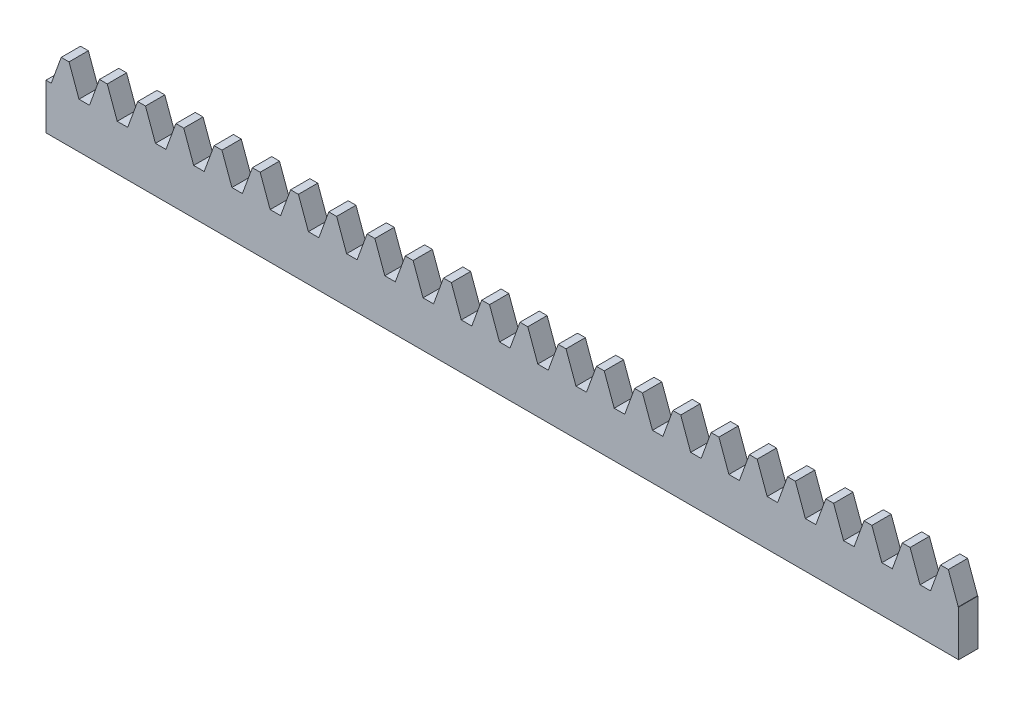
SolidWorks part; units mm, degrees
extrude "Blank" add sketch "BlankSke" against normal blind 10
sketch "BlankSke" plane through (0, 0, 0) normal (0, 0, 1) x (1, 0, 0)
  line L1 (0, 0) -> (150, 0)
  line L2 (0, 0) -> (0, 12)
  line L3 (0, 12) -> (150, 12)
  line L4 (150, 0) -> (150, 12)
  dimension "Length" = 150
  dimension "Blank_height" = 12
ref_plane "Plane1" through (0, 0, 0) normal (0, 0, 1) x (1, 0, 0)
ref_plane "Plane2" through (0, 0, 0) normal (0, 1, 0) x (1, 0, 0)
ref_plane "Plane3" through (0, 0, 0) normal (1, 0, 0) x (0, 0, -1)
sketch "HoldingSke" plane through (0, 0, 0) normal (0, 1, 0) x (1, 0, 0)
  line L0 (0, 0) -> (0.0696, 0.4951)
  line L1 (-15, 0) -> (100, 0) construction
  line L2 (0, 0) -> (-2.1039, 2.3779)
  line L3 (0, 0) -> (-11.863, 4.5341)
  line L4 (0, 0) -> (7.8269, 3.6497)
  line L5 (0, 0) -> (-23.7986, -8.8762)
  line L6 (0, 0) -> (-10.5278, -7.1032)
  line L9 (-71.009, 38.7566) -> (69.9449, 90.0596)
  line L10 (-76.2, 4.3779) -> (-66.2, 4.3779)
  line L11 (0, 0) -> (-10, 0)
  line L12 (-76.2, 101.6) -> (-76.133, 101.6)
  line L13 (24.9733, 27.94) -> (52.9518, 28.4284)
  line L14 (24.9733, 27.94) -> (24.9743, 27.94)
  line L15 (24.9733, 27.94) -> (100.4006, 29.5858)
  circle A0 centre (0, 0) radius 19.05
  circle A1 centre (0, 0) radius 5
  circle A2 centre (0, 0) radius 12.7
  dimension "MPH" = 10
  dimension "Diameter" = 38.1
  dimension "Num_teeth" = 25
  dimension "Pitch" = 0.5
  dimension "Show_teeth" = 998
  dimension "Thickness" = 12.7
  dimension "Ap" = 20
  dimension "Pitch_height" = 10
  dimension "Width" = 10
  dimension "Backlash" = 0.067
  dimension "Addendum_fac" = 1
  dimension "Dedendum_fac" = 1.25
  dimension "Clearance_fac" = 0.25
  dimension "Dedendum_add" = 0.001
  dimension "Length" = 150
  dimension "Module" = 2
sketch "TooCutSkeIll" plane through (0, 0, 0) normal (0, 0, 1) x (1, 0, 0)
  line L0 (-2.4806, 11.9474) -> (-0.9819, 7.8296)
  line L1 (-0.5111, 7.5) -> (0.5111, 7.5)
  line L2 (0.9819, 7.8296) -> (2.4806, 11.9474)
  line L3 (150, 12) -> (0, 12) construction
  line L4 (0, 0) -> (0, 64.897) construction
  line L5 (-13.208, 10) -> (12.954, 10) construction
  line L6 (0, 0) -> (150, 0) construction
  line L7 (1.7718, 10) -> (1.7718, 48.7463) construction
  line L8 (-1.7718, 10) -> (-1.7718, 48.7463) construction
  line L9 (2.5558, 12) -> (2.5558, 12.0254)
  line L10 (-2.5558, 12) -> (-2.5558, 12.0254)
  line L11 (-2.5558, 12.0254) -> (2.5558, 12.0254)
  arc A0 (0.5111, 7.5) -> (0.9819, 7.8296) centre (0.5111, 8.001) ccw
  arc A1 (-0.9819, 7.8296) -> (-0.5111, 7.5) centre (-0.5111, 8.001) ccw
  arc A2 (2.5558, 12) -> (2.4806, 11.9474) centre (2.5558, 11.92) ccw
  arc A3 (-2.4806, 11.9474) -> (-2.5558, 12) centre (-2.5558, 11.92) ccw
  dimension "Pitch_height" = 10
  dimension "Addendum_plus" = 2.0254
  dimension "Pressure_angle" = 20
  dimension "Gap_width" = 3.5436
  dimension "Dedendum" = 2.5
extrude "ToothCutIll" [suppressed] cut sketch "TooCutSkeIll" against normal through all
sketch "TooCutSkeSim" plane through (0, 0, 0) normal (0, 0, 1) x (1, 0, 0)
  line L0 (0.8619, 7.5) -> (-0.8619, 7.5)
  line L1 (2.509, 12.0254) -> (0.8619, 7.5)
  line L2 (0, 17.4625) -> (0, 53.467) construction
  line L3 (2.509, 12.0254) -> (-2.509, 12.0254)
  line L6 (-2.509, 12.0254) -> (-0.8619, 7.5)
  line L9 (-1.7718, 10) -> (1.7718, 10) construction
  line L10 (0, 0) -> (150, 0) construction
  line L11 (1.7718, 10) -> (1.7718, 53.467) construction
  line L12 (-1.7718, 10) -> (-1.7718, 53.467) construction
  dimension "Pitch_height" = 10
  dimension "Addendum_plus" = 2.0254
  dimension "Pressure_angle" = 20
  dimension "Gap_width" = 3.5436
  dimension "Dedendum" = 2.5
extrude "ToothCutSim" cut sketch "TooCutSkeSim" against normal through all
pattern_linear "TeethCuts" count 25 spacing 6.2832 along (1, 0, 0) of "ToothCutIll", "ToothCutSim"
sketch "Sketch1" plane through (0, 0, 0) normal (0, 0, 1) x (1, 0, 0)
  line L100 (150, 7.5) -> (149.9346, 7.5)
  line L101 (149.9346, 7.5) -> (148.2967, 12)
  line L102 (148.2967, 12) -> (147.013, 12)
  line L103 (147.013, 12) -> (145.3751, 7.5)
  line L104 (145.3751, 7.5) -> (143.6514, 7.5)
  line L105 (143.6514, 7.5) -> (142.0135, 12)
  line L106 (142.0135, 12) -> (140.7298, 12)
  line L107 (140.7298, 12) -> (139.0919, 7.5)
  line L108 (139.0919, 7.5) -> (137.3682, 7.5)
  line L109 (137.3682, 7.5) -> (135.7303, 12)
  line L110 (135.7303, 12) -> (134.4466, 12)
  line L111 (134.4466, 12) -> (132.8088, 7.5)
  line L112 (132.8088, 7.5) -> (131.085, 7.5)
  line L113 (131.085, 7.5) -> (129.4472, 12)
  line L114 (129.4472, 12) -> (128.1634, 12)
  line L115 (128.1634, 12) -> (126.5256, 7.5)
  line L116 (126.5256, 7.5) -> (124.8018, 7.5)
  line L117 (124.8018, 7.5) -> (123.164, 12)
  line L118 (123.164, 12) -> (121.8803, 12)
  line L119 (121.8803, 12) -> (120.2424, 7.5)
  line L120 (120.2424, 7.5) -> (118.5186, 7.5)
  line L121 (118.5186, 7.5) -> (116.8808, 12)
  line L122 (116.8808, 12) -> (115.5971, 12)
  line L123 (115.5971, 12) -> (113.9592, 7.5)
  line L124 (113.9592, 7.5) -> (112.2355, 7.5)
  line L125 (112.2355, 7.5) -> (110.5976, 12)
  line L126 (110.5976, 12) -> (109.3139, 12)
  line L127 (109.3139, 12) -> (107.676, 7.5)
  line L128 (107.676, 7.5) -> (105.9523, 7.5)
  line L129 (105.9523, 7.5) -> (104.3144, 12)
  line L130 (104.3144, 12) -> (103.0307, 12)
  line L131 (103.0307, 12) -> (101.3928, 7.5)
  line L132 (101.3928, 7.5) -> (99.6691, 7.5)
  line L133 (99.6691, 7.5) -> (98.0312, 12)
  line L134 (98.0312, 12) -> (96.7475, 12)
  line L135 (96.7475, 12) -> (95.1097, 7.5)
  line L136 (95.1097, 7.5) -> (93.3859, 7.5)
  line L137 (93.3859, 7.5) -> (91.748, 12)
  line L138 (91.748, 12) -> (90.4643, 12)
  line L139 (90.4643, 12) -> (88.8265, 7.5)
  line L140 (88.8265, 7.5) -> (87.1027, 7.5)
  line L141 (87.1027, 7.5) -> (85.4649, 12)
  line L142 (85.4649, 12) -> (84.1811, 12)
  line L143 (84.1811, 12) -> (82.5433, 7.5)
  line L144 (82.5433, 7.5) -> (80.8195, 7.5)
  line L145 (80.8195, 7.5) -> (79.1817, 12)
  line L146 (79.1817, 12) -> (77.898, 12)
  line L147 (77.898, 12) -> (76.2601, 7.5)
  line L148 (76.2601, 7.5) -> (74.5364, 7.5)
  line L149 (74.5364, 7.5) -> (72.8985, 12)
  line L150 (72.8985, 12) -> (71.6148, 12)
  line L151 (71.6148, 12) -> (69.9769, 7.5)
  line L152 (69.9769, 7.5) -> (68.2532, 7.5)
  line L153 (68.2532, 7.5) -> (66.6153, 12)
  line L154 (66.6153, 12) -> (65.3316, 12)
  line L155 (65.3316, 12) -> (63.6937, 7.5)
  line L156 (63.6937, 7.5) -> (61.97, 7.5)
  line L157 (61.97, 7.5) -> (60.3321, 12)
  line L158 (60.3321, 12) -> (59.0484, 12)
  line L159 (59.0484, 12) -> (57.4105, 7.5)
  line L160 (57.4105, 7.5) -> (55.6868, 7.5)
  line L161 (55.6868, 7.5) -> (54.0489, 12)
  line L162 (54.0489, 12) -> (52.7652, 12)
  line L163 (52.7652, 12) -> (51.1274, 7.5)
  line L164 (51.1274, 7.5) -> (49.4036, 7.5)
  line L165 (49.4036, 7.5) -> (47.7657, 12)
  line L166 (47.7657, 12) -> (46.482, 12)
  line L167 (46.482, 12) -> (44.8442, 7.5)
  line L168 (44.8442, 7.5) -> (43.1204, 7.5)
  line L169 (43.1204, 7.5) -> (41.4826, 12)
  line L170 (41.4826, 12) -> (40.1988, 12)
  line L171 (40.1988, 12) -> (38.561, 7.5)
  line L172 (38.561, 7.5) -> (36.8372, 7.5)
  line L173 (36.8372, 7.5) -> (35.1994, 12)
  line L174 (35.1994, 12) -> (33.9157, 12)
  line L175 (33.9157, 12) -> (32.2778, 7.5)
  line L176 (32.2778, 7.5) -> (30.5541, 7.5)
  line L177 (30.5541, 7.5) -> (28.9162, 12)
  line L178 (28.9162, 12) -> (27.6325, 12)
  line L179 (27.6325, 12) -> (25.9946, 7.5)
  line L180 (25.9946, 7.5) -> (24.2709, 7.5)
  line L181 (24.2709, 7.5) -> (22.633, 12)
  line L182 (22.633, 12) -> (21.3493, 12)
  line L183 (21.3493, 12) -> (19.7114, 7.5)
  line L184 (19.7114, 7.5) -> (17.9877, 7.5)
  line L185 (17.9877, 7.5) -> (16.3498, 12)
  line L186 (16.3498, 12) -> (15.0661, 12)
  line L187 (15.0661, 12) -> (13.4282, 7.5)
  line L188 (13.4282, 7.5) -> (11.7045, 7.5)
  line L189 (11.7045, 7.5) -> (10.0666, 12)
  line L190 (10.0666, 12) -> (8.7829, 12)
  line L191 (8.7829, 12) -> (7.1451, 7.5)
  line L192 (7.1451, 7.5) -> (5.4213, 7.5)
  line L193 (5.4213, 7.5) -> (3.7834, 12)
  line L194 (3.7834, 12) -> (2.4997, 12)
  line L195 (2.4997, 12) -> (0.8619, 7.5)
  line L196 (0.8619, 7.5) -> (0, 7.5)
  line L197 (0, 7.5) -> (0, 0)
  line L198 (0, 0) -> (150, 0)
  line L199 (150, 0) -> (150, 7.5)
  line L200 (150, 7.5) -> (149.9346, 7.5)
  line L201 (149.9346, 7.5) -> (148.2967, 12)
  line L202 (148.2967, 12) -> (147.013, 12)
  line L203 (147.013, 12) -> (145.3751, 7.5)
  line L204 (145.3751, 7.5) -> (143.6514, 7.5)
  line L205 (143.6514, 7.5) -> (142.0135, 12)
  line L206 (142.0135, 12) -> (140.7298, 12)
  line L207 (140.7298, 12) -> (139.0919, 7.5)
  line L208 (139.0919, 7.5) -> (137.3682, 7.5)
  line L209 (137.3682, 7.5) -> (135.7303, 12)
  line L210 (135.7303, 12) -> (134.4466, 12)
  line L211 (134.4466, 12) -> (132.8088, 7.5)
  line L212 (132.8088, 7.5) -> (131.085, 7.5)
  line L213 (131.085, 7.5) -> (129.4472, 12)
  line L214 (129.4472, 12) -> (128.1634, 12)
  line L215 (128.1634, 12) -> (126.5256, 7.5)
  line L216 (126.5256, 7.5) -> (124.8018, 7.5)
  line L217 (124.8018, 7.5) -> (123.164, 12)
  line L218 (123.164, 12) -> (121.8803, 12)
  line L219 (121.8803, 12) -> (120.2424, 7.5)
  line L220 (120.2424, 7.5) -> (118.5186, 7.5)
  line L221 (118.5186, 7.5) -> (116.8808, 12)
  line L222 (116.8808, 12) -> (115.5971, 12)
  line L223 (115.5971, 12) -> (113.9592, 7.5)
  line L224 (113.9592, 7.5) -> (112.2355, 7.5)
  line L225 (112.2355, 7.5) -> (110.5976, 12)
  line L226 (110.5976, 12) -> (109.3139, 12)
  line L227 (109.3139, 12) -> (107.676, 7.5)
  line L228 (107.676, 7.5) -> (105.9523, 7.5)
  line L229 (105.9523, 7.5) -> (104.3144, 12)
  line L230 (104.3144, 12) -> (103.0307, 12)
  line L231 (103.0307, 12) -> (101.3928, 7.5)
  line L232 (101.3928, 7.5) -> (99.6691, 7.5)
  line L233 (99.6691, 7.5) -> (98.0312, 12)
  line L234 (98.0312, 12) -> (96.7475, 12)
  line L235 (96.7475, 12) -> (95.1097, 7.5)
  line L236 (95.1097, 7.5) -> (93.3859, 7.5)
  line L237 (93.3859, 7.5) -> (91.748, 12)
  line L238 (91.748, 12) -> (90.4643, 12)
  line L239 (90.4643, 12) -> (88.8265, 7.5)
  line L240 (88.8265, 7.5) -> (87.1027, 7.5)
  line L241 (87.1027, 7.5) -> (85.4649, 12)
  line L242 (85.4649, 12) -> (84.1811, 12)
  line L243 (84.1811, 12) -> (82.5433, 7.5)
  line L244 (82.5433, 7.5) -> (80.8195, 7.5)
  line L245 (80.8195, 7.5) -> (79.1817, 12)
  line L246 (79.1817, 12) -> (77.898, 12)
  line L247 (77.898, 12) -> (76.2601, 7.5)
  line L248 (76.2601, 7.5) -> (74.5364, 7.5)
  line L249 (74.5364, 7.5) -> (72.8985, 12)
  line L250 (72.8985, 12) -> (71.6148, 12)
  line L251 (71.6148, 12) -> (69.9769, 7.5)
  line L252 (69.9769, 7.5) -> (68.2532, 7.5)
  line L253 (68.2532, 7.5) -> (66.6153, 12)
  line L254 (66.6153, 12) -> (65.3316, 12)
  line L255 (65.3316, 12) -> (63.6937, 7.5)
  line L256 (63.6937, 7.5) -> (61.97, 7.5)
  line L257 (61.97, 7.5) -> (60.3321, 12)
  line L258 (60.3321, 12) -> (59.0484, 12)
  line L259 (59.0484, 12) -> (57.4105, 7.5)
  line L260 (57.4105, 7.5) -> (55.6868, 7.5)
  line L261 (55.6868, 7.5) -> (54.0489, 12)
  line L262 (54.0489, 12) -> (52.7652, 12)
  line L263 (52.7652, 12) -> (51.1274, 7.5)
  line L264 (51.1274, 7.5) -> (49.4036, 7.5)
  line L265 (49.4036, 7.5) -> (47.7657, 12)
  line L266 (47.7657, 12) -> (46.482, 12)
  line L267 (46.482, 12) -> (44.8442, 7.5)
  line L268 (44.8442, 7.5) -> (43.1204, 7.5)
  line L269 (43.1204, 7.5) -> (41.4826, 12)
  line L270 (41.4826, 12) -> (40.1988, 12)
  line L271 (40.1988, 12) -> (38.561, 7.5)
  line L272 (38.561, 7.5) -> (36.8372, 7.5)
  line L273 (36.8372, 7.5) -> (35.1994, 12)
  line L274 (35.1994, 12) -> (33.9157, 12)
  line L275 (33.9157, 12) -> (32.2778, 7.5)
  line L276 (32.2778, 7.5) -> (30.5541, 7.5)
  line L277 (30.5541, 7.5) -> (28.9162, 12)
  line L278 (28.9162, 12) -> (27.6325, 12)
  line L279 (27.6325, 12) -> (25.9946, 7.5)
  line L280 (25.9946, 7.5) -> (24.2709, 7.5)
  line L281 (24.2709, 7.5) -> (22.633, 12)
  line L282 (22.633, 12) -> (21.3493, 12)
  line L283 (21.3493, 12) -> (19.7114, 7.5)
  line L284 (19.7114, 7.5) -> (17.9877, 7.5)
  line L285 (17.9877, 7.5) -> (16.3498, 12)
  line L286 (16.3498, 12) -> (15.0661, 12)
  line L287 (15.0661, 12) -> (13.4282, 7.5)
  line L288 (13.4282, 7.5) -> (11.7045, 7.5)
  line L289 (11.7045, 7.5) -> (10.0666, 12)
  line L290 (10.0666, 12) -> (8.7829, 12)
  line L291 (8.7829, 12) -> (7.1451, 7.5)
  line L292 (7.1451, 7.5) -> (5.4213, 7.5)
  line L293 (5.4213, 7.5) -> (3.7834, 12)
  line L294 (3.7834, 12) -> (2.4997, 12)
  line L295 (2.4997, 12) -> (0.8619, 7.5)
  line L296 (0.8619, 7.5) -> (0, 7.5)
  line L297 (0, 7.5) -> (0, 0)
  line L298 (0, 0) -> (150, 0)
  line L299 (150, 0) -> (150, 7.5)
  dimension "D1" = 0
extrude "Cut-Extrude1" cut sketch "Sketch1" against normal blind 6.825
equation "' \"Module@HoldingSke\" = 6.35"
equation "' \"Num_teeth@HoldingSke\" = 12"
equation "' \"Ap@HoldingSke\" =  20"
equation "' \"Ap@HoldingSke\" = 20"
equation "' \"Width@HoldingSke\" = 0.25 * 25.4"
equation "' \"Show_teeth@HoldingSke\" = 500"
equation "' \"Backlash@HoldingSke\" = 0.009 * 25.4"
equation "' \"Addendum_fac@HoldingSke\" = 1.0"
equation "' \"Dedendum_fac@HoldingSke\" = 1.25"
equation "' \"Dedendum_add@HoldingSke\" = 0.00005 * 25.4"
equation "' \"Clearance_fac@HoldingSke\" = 0.25"
equation "' \"Pitch_height@HoldingSke\" = 1 * 25.4"
equation "' \"Length@HoldingSke\" = 4.71 * 25.4"
equation "\"Pitch@HoldingSke\" = 1 / \"Module@HoldingSke\""
equation "\"MPH@HoldingSke\" = \"Dedendum_fac@HoldingSke\" / \"Pitch@HoldingSke\" + 2 * \"Dedendum_add@HoldingSke\" + 0.002 * 25.4"
equation "\"MPH@HoldingSke\" = ((sgn( \"MPH@HoldingSke\" - \"Pitch_height@HoldingSke\")+1)*( \"MPH@HoldingSke\" - \"Pitch_height@HoldingSke\"))/2 + \"Pitch_height@HoldingSke\""
equation "\"Blank_height@BlankSke\" = \"Pitch_height@HoldingSke\" + \"Addendum_fac@HoldingSke\"  / \"Pitch@HoldingSke\" "
equation "\"Length@BlankSke\" =  \"Length@HoldingSke\""
equation "\"Face_width@Blank\" = \"Width@HoldingSke\""
equation "\"Pressure_angle@TooCutSkeIll\" = \"Ap@HoldingSke\""
equation "\"Addendum_plus@TooCutSkeIll\" =  \"Addendum_fac@HoldingSke\"  / \"Pitch@HoldingSke\" + 0.001 *25.4"
equation "\"Dedendum@TooCutSkeIll\" = \"Dedendum_fac@HoldingSke\"  / \"Pitch@HoldingSke\""
equation "\"Pitch_height@TooCutSkeIll\" =  \"MPH@HoldingSke\""
equation "\"Gap_width@TooCutSkeIll\" = 3.14159265 / 2 / \"Pitch@HoldingSke\" + 6 * \"Backlash@HoldingSke\""
equation "\"Pressure_angle@TooCutSkeSim\" = \"Ap@HoldingSke\""
equation "\"Addendum_plus@TooCutSkeSim\" =  \"Addendum_fac@HoldingSke\"  / \"Pitch@HoldingSke\" + 0.001 * 25.4"
equation "\"Dedendum@TooCutSkeSim\" = \"Dedendum_fac@HoldingSke\"  / \"Pitch@HoldingSke\""
equation "\"Pitch_height@TooCutSkeSim\" =  \"MPH@HoldingSke\""
equation "\"Gap_width@TooCutSkeSim\" = 3.14159265 / 2 / \"Pitch@HoldingSke\" + 6 * \"Backlash@HoldingSke\""
equation "\"Root_fillet@TooCutSkeIll\" = \"Clearance_fac@HoldingSke\" / \"Pitch@HoldingSke\" + \"Dedendum_add@HoldingSke\""
equation "\"Break_rad@TooCutSkeIll\" = 0.02 / \"Pitch@HoldingSke\" * 2"
equation "\"Linear_pitch@TeethCuts\" = 3.14159265 / \"Pitch@HoldingSke\""
equation "\"Num_teeth@HoldingSke\" = int( ( \"Length@HoldingSke\" + 0 ) / (3.14159265 / \"Pitch@HoldingSke\")) + 0.9999  + 1"
equation " \"Num_teeth@TeethCuts\" = int( \"Show_teeth@HoldingSke\" ) + 1"
equation " \"Num_teeth@TeethCuts\" = ((sgn( \"Num_teeth@TeethCuts\" - \"Num_teeth@HoldingSke\" )-1)*( \"Num_teeth@TeethCuts\" - \"Num_teeth@HoldingSke\" ))/-2+ \"Num_teeth@HoldingSke\""
equation " \"Num_teeth@TeethCuts\" = ((sgn( \"Num_teeth@TeethCuts\" - 2.0)+1)*( \"Num_teeth@TeethCuts\" - 2.0))/2 +2.0"
